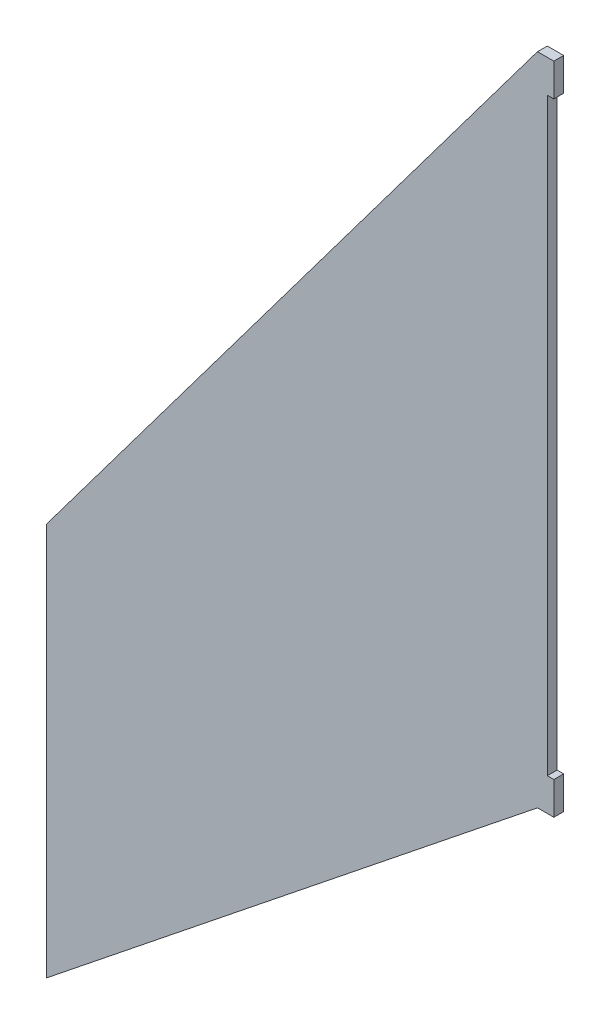
SolidWorks part; units mm, degrees
ref_plane "Plan de face" through (0, 0, 0) normal (0, 0, 1) x (1, 0, 0)
ref_plane "Plan de dessus" through (0, 0, 0) normal (0, 1, 0) x (1, 0, 0)
ref_plane "Plan de droite" through (0, 0, 0) normal (1, 0, 0) x (0, 0, -1)
sketch "Esquisse1" plane through (0, 0, 0) normal (0, 0, 1) x (1, 0, 0)
  line L0 (0, 0) -> (-5, 0)
  line L1 (-5, 0) -> (-155, -200)
  line L2 (-155, -200) -> (-155, -320)
  line L3 (-155, -320) -> (-5, -200)
  line L4 (-5, -200) -> (0, -200)
  line L5 (0, -200) -> (0, -190)
  line L6 (0, -190) -> (-2, -190)
  line L7 (0, 0) -> (0, -10)
  line L8 (0, -10) -> (-2, -10)
  line L9 (-2, -10) -> (-2, -190)
  point P3 (-8.0172, -200)
  point P12 (-8.0204, -200)
  point P13 (5.8808, -200)
  point P14 (-10.321, -200)
  dimension "D1" = 5
  dimension "D2" = 10
  dimension "D3" = 180
  dimension "D4" = 120
  dimension "D5" = 250
  dimension "D6" = 150
  dimension "D7" = 2
  dimension "D8" = 5
  dimension "D9" = 2
extrude "Boss.-Extru.1" add sketch "Esquisse1" along normal blind 3
